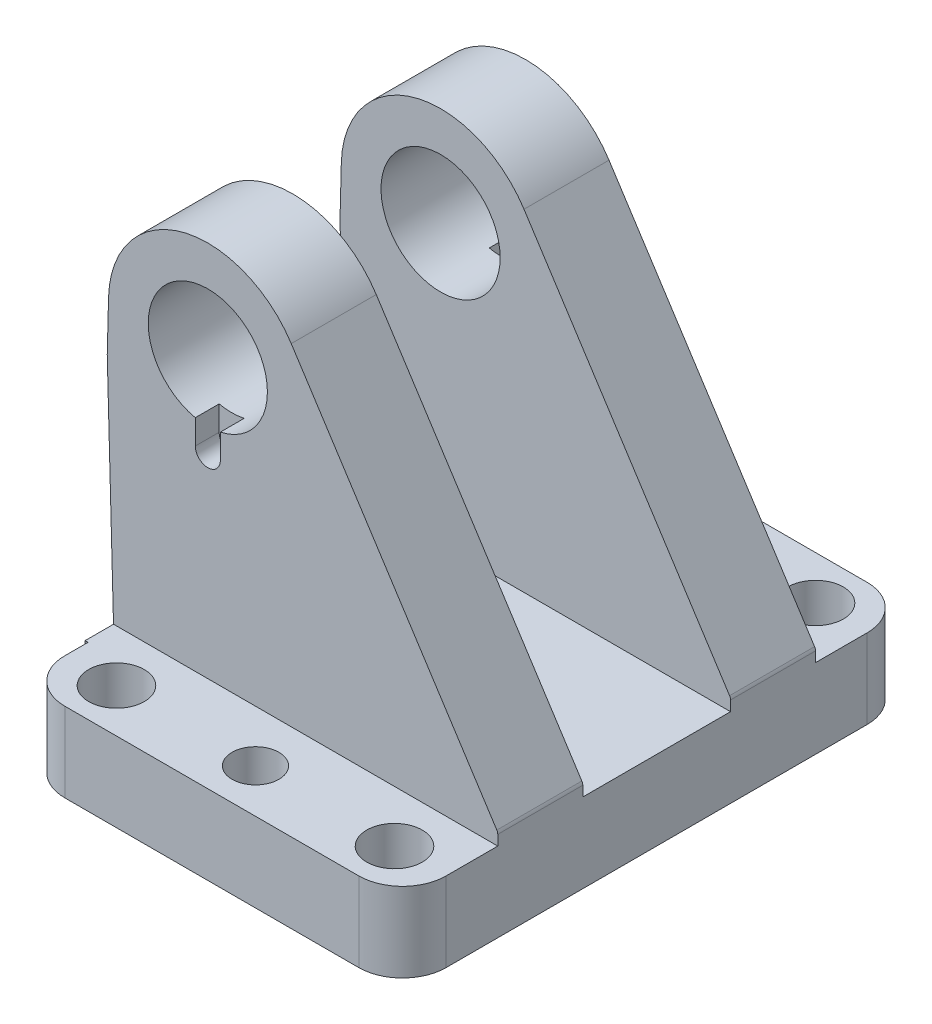
SolidWorks part; units mm, degrees
ref_plane "Front Plane" through (0, 0, 0) normal (0, 0, 1) x (1, 0, 0)
ref_plane "Top Plane" through (0, 0, 0) normal (0, 1, 0) x (1, 0, 0)
ref_plane "Right Plane" through (0, 0, 0) normal (1, 0, 0) x (0, 0, -1)
ref_plane "Plane1" through (0, 0, 0) normal (0, 1, 0) x (1, 0, 0)
sketch "Sketch1" plane through (0, 0, 0) normal (0, 1, 0) x (1, 0, 0)
  line L0 (-37, -64) -> (37, -64)
  line L1 (48, -53) -> (48, 53)
  line L2 (37, 64) -> (-37, 64)
  line L3 (-48, 53) -> (-48, -53)
  arc A0 (-48, -53) -> (-37, -64) centre (-37, -53) ccw
  arc A1 (37, -64) -> (48, -53) centre (37, -53) ccw
  arc A2 (48, 53) -> (37, 64) centre (37, 53) ccw
  arc A3 (-37, 64) -> (-48, 53) centre (-37, 53) ccw
  circle A4 centre (35, 53) radius 7
  circle A5 centre (35, -53) radius 7
  circle A6 centre (0, 53) radius 5.9
  circle A7 centre (0, -53) radius 5.9
  circle A8 centre (-35, 53) radius 7
  circle A9 centre (-35, -53) radius 7
extrude "Boss-Extrude1" add sketch "Sketch1" along normal blind 20
ref_plane "Plane2" through (0, 0, 0) normal (0, 0, 1) x (1, 0, 0)
sketch "Sketch2" plane through (0, 0, 0) normal (0, 0, 1) x (1, 0, 0)
  line L0 (-48.7443, 20) -> (-48.2, 0)
  line L1 (-48.2, 0) -> (-43.2, 0)
  line L2 (-43.2, 0) -> (-43.2, 20)
  line L3 (-43.2, 20) -> (-48.7443, 20)
extrude "Boss-Extrude2" add sketch "Sketch2" against normal blind 47.15 and the other way blind 47.15
ref_plane "Plane3" through (0, 0, 40) normal (0, 0, 1) x (1, 0, 0)
sketch "Sketch3" plane through (0, 0, 40) normal (0, 0, 1) x (1, 0, 0)
  line L0 (-50.3228, 77.9985) -> (-48.2, 0)
  line L1 (-48.2, 0) -> (48, 0)
  line L2 (48, 0) -> (48, 22.558)
  line L3 (47.7603, 23.3714) -> (-3.9953, 103.5574)
  line L4 (-49.9914, 90.6544) -> (-50.3228, 77.9985)
  arc A0 (48, 22.558) -> (47.7603, 23.3714) centre (46.5, 22.558) ccw
  arc A1 (-3.9953, 103.5574) -> (-49.9914, 90.6544) centre (-25, 90) ccw
  circle A2 centre (-25, 90) radius 15
extrude "Boss-Extrude3" add sketch "Sketch3" against normal blind 21.4
ref_plane "Plane4" through (0, 0, -40) normal (0, 0, 1) x (1, 0, 0)
sketch "Sketch4" plane through (0, 0, -40) normal (0, 0, 1) x (1, 0, 0)
  line L0 (-50.3228, 77.9985) -> (-48.2, 0)
  line L1 (-48.2, 0) -> (48, 0)
  line L2 (48, 0) -> (48, 22.558)
  line L3 (47.7603, 23.3714) -> (-3.9953, 103.5574)
  line L4 (-49.9914, 90.6544) -> (-50.3228, 77.9985)
  arc A0 (48, 22.558) -> (47.7603, 23.3714) centre (46.5, 22.558) ccw
  arc A1 (-3.9953, 103.5574) -> (-49.9914, 90.6544) centre (-25, 90) ccw
  circle A2 centre (-25, 90) radius 15
extrude "Boss-Extrude4" add sketch "Sketch4" along normal blind 21.4
ref_plane "Plane5" through (0, 0, 40) normal (0, 0, 1) x (1, 0, 0)
sketch "Sketch5" plane through (0, 0, 40) normal (0, 0, 1) x (1, 0, 0)
  line L0 (-21.85, 69.15) -> (-21.85, 90)
  line L1 (-21.85, 90) -> (-28.15, 90)
  line L2 (-28.15, 90) -> (-28.15, 69.15)
  arc A0 (-28.15, 69.15) -> (-21.85, 69.15) centre (-25, 69.15) ccw
extrude "Cut-Extrude1" cut sketch "Sketch5" against normal blind 6 and the other way blind 6
ref_plane "Plane6" through (0, 0, -40) normal (0, 0, 1) x (1, 0, 0)
sketch "Sketch6" plane through (0, 0, -40) normal (0, 0, 1) x (1, 0, 0)
  line L0 (-21.85, 69.15) -> (-21.85, 90)
  line L1 (-21.85, 90) -> (-28.15, 90)
  line L2 (-28.15, 90) -> (-28.15, 69.15)
  arc A0 (-28.15, 69.15) -> (-21.85, 69.15) centre (-25, 69.15) ccw
extrude "Cut-Extrude2" cut sketch "Sketch6" against normal blind 6 and the other way blind 6
